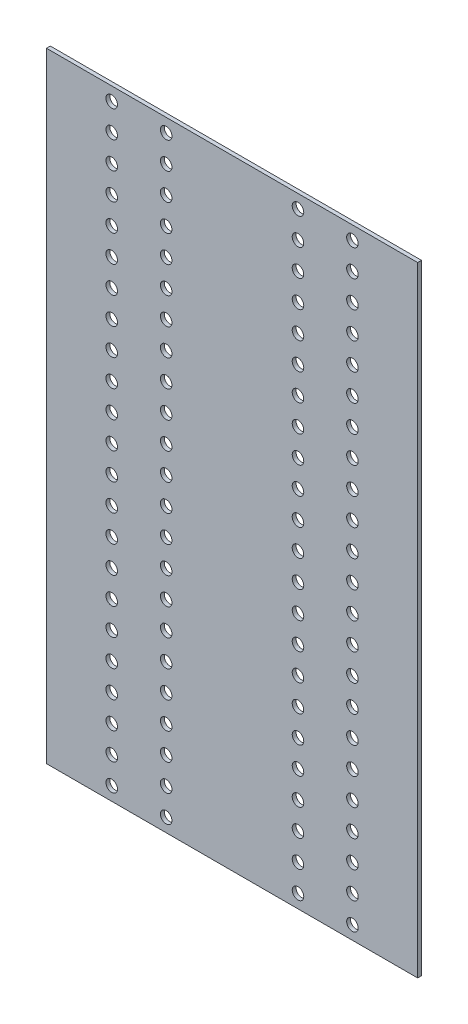
SolidWorks part; units mm, degrees
ref_plane "Front" through (0, 0, 0) normal (0, 0, 1) x (1, 0, 0)
ref_plane "Top" through (0, 0, 0) normal (0, 1, 0) x (1, 0, 0)
ref_plane "Right" through (0, 0, 0) normal (1, 0, 0) x (0, 0, -1)
sketch "Sketch1" plane through (0, 0, 0) normal (0, 0, 1) x (1, 0, 0)
  line L1 (0, 0) -> (289.4, 0)
  line L2 (0, 0) -> (0, 483)
  line L3 (0, 483) -> (289.4, 483)
  line L4 (289.4, 0) -> (289.4, 483)
  dimension "D1" = 289.4
  dimension "D2" = 483
extrude "Boss-Extrude1" add sketch "Sketch1" along normal blind 3
hole_wizard "M8 Clearance Hole1" positions "Sketch2" profile "Sketch3" hole size "M8" standard "ANSI Metric" end condition through all
sketch "Sketch2" plane through (0, 0, 3) normal (0, 0, 1) x (1, 0, 0)
  line L0 (0, 0) -> (289.4, 0) construction
  line L1 (289.4, 0) -> (289.4, 483) construction
  line L2 (0, 483) -> (0, 0) construction
  point P0 (238.52, 10.5)
  point P2 (196.08, 10.5)
  point P4 (93.32, 10.5)
  point P6 (50.88, 10.5)
  point P21 (238.52, 31.5)
  point P22 (196.08, 31.5)
  point P23 (93.32, 31.5)
  point P24 (50.88, 31.5)
  point P25 (238.52, 52.5)
  point P26 (196.08, 52.5)
  point P27 (93.32, 52.5)
  point P28 (50.88, 52.5)
  point P29 (238.52, 73.5)
  point P30 (196.08, 73.5)
  point P31 (93.32, 73.5)
  point P32 (50.88, 73.5)
  point P33 (238.52, 94.5)
  point P34 (196.08, 94.5)
  point P35 (93.32, 94.5)
  point P36 (50.88, 94.5)
  point P37 (238.52, 115.5)
  point P38 (196.08, 115.5)
  point P39 (93.32, 115.5)
  point P40 (50.88, 115.5)
  point P41 (238.52, 136.5)
  point P42 (196.08, 136.5)
  point P43 (93.32, 136.5)
  point P44 (50.88, 136.5)
  point P45 (238.52, 157.5)
  point P46 (196.08, 157.5)
  point P47 (93.32, 157.5)
  point P48 (50.88, 157.5)
  point P49 (238.52, 178.5)
  point P50 (196.08, 178.5)
  point P51 (93.32, 178.5)
  point P52 (50.88, 178.5)
  point P53 (238.52, 199.5)
  point P54 (196.08, 199.5)
  point P55 (93.32, 199.5)
  point P56 (50.88, 199.5)
  point P57 (238.52, 220.5)
  point P58 (196.08, 220.5)
  point P59 (93.32, 220.5)
  point P60 (50.88, 220.5)
  point P61 (238.52, 241.5)
  point P62 (196.08, 241.5)
  point P63 (93.32, 241.5)
  point P64 (50.88, 241.5)
  point P65 (238.52, 262.5)
  point P66 (196.08, 262.5)
  point P67 (93.32, 262.5)
  point P68 (50.88, 262.5)
  point P69 (238.52, 283.5)
  point P70 (196.08, 283.5)
  point P71 (93.32, 283.5)
  point P72 (50.88, 283.5)
  point P73 (238.52, 304.5)
  point P74 (196.08, 304.5)
  point P75 (93.32, 304.5)
  point P76 (50.88, 304.5)
  point P77 (238.52, 325.5)
  point P78 (196.08, 325.5)
  point P79 (93.32, 325.5)
  point P80 (50.88, 325.5)
  point P81 (238.52, 346.5)
  point P82 (196.08, 346.5)
  point P83 (93.32, 346.5)
  point P84 (50.88, 346.5)
  point P85 (238.52, 367.5)
  point P86 (196.08, 367.5)
  point P87 (93.32, 367.5)
  point P88 (50.88, 367.5)
  point P89 (238.52, 388.5)
  point P90 (196.08, 388.5)
  point P91 (93.32, 388.5)
  point P92 (50.88, 388.5)
  point P93 (238.52, 409.5)
  point P94 (196.08, 409.5)
  point P95 (93.32, 409.5)
  point P96 (50.88, 409.5)
  point P97 (238.52, 430.5)
  point P98 (196.08, 430.5)
  point P99 (93.32, 430.5)
  point P100 (50.88, 430.5)
  point P101 (238.52, 451.5)
  point P102 (196.08, 451.5)
  point P103 (93.32, 451.5)
  point P104 (50.88, 451.5)
  point P105 (238.52, 472.5)
  point P106 (196.08, 472.5)
  point P107 (93.32, 472.5)
  point P108 (50.88, 472.5)
  dimension "D1" = 10.5
  dimension "D2" = 50.88
  dimension "D3" = 42.44
  dimension "D5" = 50.88
  dimension "D6" = 42.44
  dimension "D4" = 23
sketch "Sketch3" plane through (238.52, 10.5, 3) normal (1, 0, 0) x (0, -1, 0)
  line L0 (0, 0) -> (0, 3)
  line L1 (0, 3) -> (4.5, 3)
  line L2 (4.5, 3) -> (4.5, 0)
  line L5 (4.5, 0) -> (0, 0)
  line L11 (0, -6.35) -> (0, 107.95) construction
  dimension "Thru Hole Dia." = 9
  dimension "Thru Hole Depth" = 3
